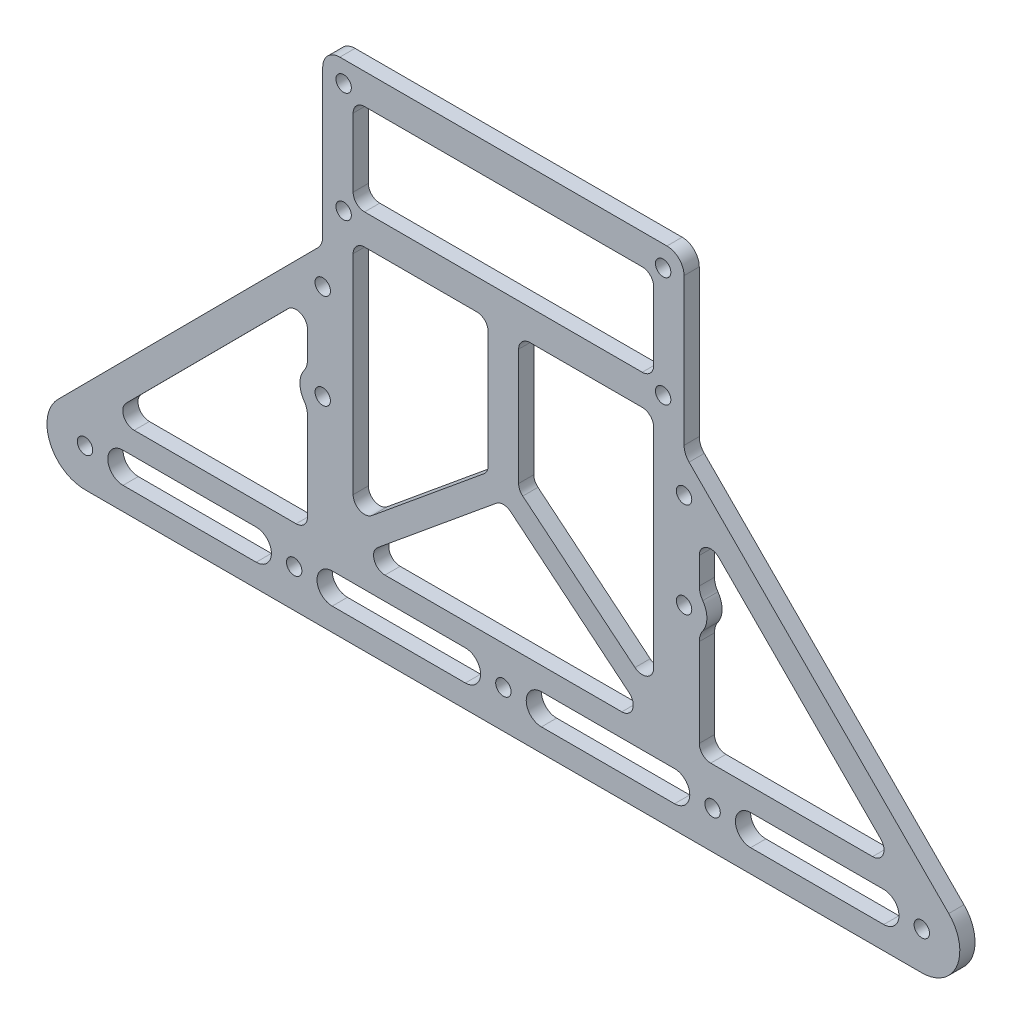
SolidWorks part; units mm, degrees
material "Thornel Mat VMA"
ref_plane "前视基准面" through (0, 0, 0) normal (0, 0, 1) x (1, 0, 0)
ref_plane "上视基准面" through (0, 0, 0) normal (0, 1, 0) x (1, 0, 0)
ref_plane "右视基准面" through (0, 0, 0) normal (1, 0, 0) x (0, 0, -1)
other "Configuration Table"
sketch "草图1" plane through (0, 0, 0) normal (0, 0, 1) x (1, 0, 0)
  line L0 (0, -34.5287) -> (0, -50034.5287) construction
  line L1 (-47.5, -20) -> (47.5, -20)
  line L2 (-47.5, -20) -> (-47.5, 20)
  line L3 (-47.5, 20) -> (47.5, 20)
  line L4 (47.5, -20) -> (47.5, 20)
  line L5 (-47.5, -20) -> (47.5, 20) construction
  line L6 (-47.5, 20) -> (47.5, -20) construction
  line L7 (-42, -14.5) -> (42, -14.5) construction
  line L8 (-42, -14.5) -> (-42, 14.5) construction
  line L9 (-42, 14.5) -> (42, 14.5) construction
  line L10 (42, -14.5) -> (42, 14.5) construction
  line L11 (-42, -14.5) -> (42, 14.5) construction
  line L12 (-42, 14.5) -> (42, -14.5) construction
  line L13 (-47.5, -20) -> (-47.5, -25)
  line L18 (110, -102) -> (-110, -102) construction
  line L19 (110, -112) -> (-110, -112)
  line L20 (-47.5, -25) -> (-117.0892, -94.9471)
  line L21 (110, -92) -> (-110, -92)
  line L22 (47.5, -25) -> (117.0892, -94.9471)
  line L23 (47.5, -20) -> (47.5, -25)
  circle A0 centre (-42, 14.5) radius 2.025
  circle A1 centre (42, 14.5) radius 2.025
  circle A2 centre (42, -14.5) radius 2.025
  circle A3 centre (-42, -14.5) radius 2.025
  circle A4 centre (-42, 14.5) radius 5.5 construction
  arc A5 (110, -112) -> (110, -92) centre (110, -102) ccw
  arc A6 (-110, -92) -> (-110, -112) centre (-110, -102) ccw
  circle A7 centre (-110, -102) radius 2.025
  circle A8 centre (-55, -102) radius 2.025
  circle A9 centre (0, -102) radius 2.025
  circle A10 centre (55, -102) radius 2.025
  circle A11 centre (110, -102) radius 2.025
  point P0 (0, 0)
  point P6 (0, 0)
  point P17 (0, -102)
  point P20 (0, -102)
  dimension "D3" = 4.05
  dimension "D7" = 11
  dimension "D8" = 5
  dimension "D6" = 4.05
  dimension "D1" = 40
  dimension "D2" = 95
  dimension "D4" = 220
  dimension "D5" = 20
  dimension "D9" = 92
  dimension "D10" = 5
extrude "凸台-拉伸1" add sketch "草图1" along normal blind 4 contours L1 L4 L3 L2 A3 A2 A1 A0 | A6 L21 A5 L22 L23 L1 L13 L20 | L21 A6 L19 A5 A11 A10 A9 A8 A7
fillet "圆角1" radius 4.5 4 edges at (-47.5, -25, 2) (47.5, 20, 2) (47.5, -25, 2) (-47.5, 20, 2)
sketch "草图2" plane through (0, 0, 4) normal (0, 0, 1) x (1, 0, 0)
  line L0 (-43, 20) -> (43, 20) construction
  line L1 (-39.5, -12) -> (39.5, -12)
  line L2 (-39.5, -12) -> (-39.5, 12)
  line L3 (-39.5, 12) -> (39.5, 12)
  line L4 (39.5, -12) -> (39.5, 12)
  line L5 (-39.5, -12) -> (39.5, 12) construction
  line L6 (-39.5, 12) -> (39.5, -12) construction
  line L7 (-47.5, -23.1428) -> (-47.5, 15.5) construction
  line L8 (0, 0) -> (0, -50000) construction
  line L9 (-39.5, -20) -> (-4, -20)
  line L10 (-4, -20) -> (-4, -55)
  line L11 (-4, -55) -> (-39.5, -84.2281)
  line L12 (-39.5, -84.2281) -> (-39.5, -20)
  line L13 (0, -59.4786) -> (-39.5, -92)
  line L14 (-39.5, -92) -> (39.5, -92)
  line L15 (0, -92) -> (0, -59.4786)
  line L16 (110, -112) -> (-110, -112) construction
  line L17 (-39.5, -84.2281) -> (-39.5, -92) construction
  line L18 (-51.5, -38.9456) -> (-104.283, -92)
  line L19 (-104.283, -92) -> (-51.5, -92)
  line L20 (-51.5, -92) -> (-51.5, -38.9456)
  line L21 (-48.8099, -26.3166) -> (-117.0892, -94.9471) construction
  line L22 (104.283, -92) -> (51.5, -92)
  line L23 (51.5, -38.9456) -> (104.283, -92)
  line L24 (51.5, -92) -> (51.5, -38.9456)
  line L25 (0, -59.4786) -> (39.5, -92)
  line L26 (4, -55) -> (39.5, -84.2281)
  line L27 (4, -20) -> (4, -55)
  line L28 (39.5, -20) -> (4, -20)
  line L29 (39.5, -84.2281) -> (39.5, -20)
  line L30 (-110, -102) -> (-55, -102) construction
  line L31 (-100, -102) -> (-65, -102) construction
  line L32 (-100, -98) -> (-65, -98)
  line L33 (-100, -106) -> (-65, -106)
  line L34 (-45, -102) -> (-10, -102) construction
  line L35 (-45, -98) -> (-10, -98)
  line L36 (-45, -106) -> (-10, -106)
  line L37 (10, -102) -> (45, -102) construction
  line L38 (10, -98) -> (45, -98)
  line L39 (10, -106) -> (45, -106)
  line L40 (65, -102) -> (100, -102) construction
  line L41 (65, -98) -> (100, -98)
  line L42 (65, -106) -> (100, -106)
  line L43 (55, -102) -> (110, -102) construction
  arc A0 (-100, -98) -> (-100, -106) centre (-100, -102) ccw
  arc A1 (-65, -106) -> (-65, -98) centre (-65, -102) ccw
  arc A2 (-45, -98) -> (-45, -106) centre (-45, -102) ccw
  arc A3 (-10, -106) -> (-10, -98) centre (-10, -102) ccw
  arc A4 (10, -98) -> (10, -106) centre (10, -102) ccw
  arc A5 (45, -106) -> (45, -98) centre (45, -102) ccw
  arc A6 (65, -98) -> (65, -106) centre (65, -102) ccw
  arc A7 (100, -106) -> (100, -98) centre (100, -102) ccw
  point P0 (0, 0)
  point P40 (-82.5, -102)
  point P48 (-27.5, -102)
  point P55 (27.5, -102)
  point P62 (82.5, -102)
  point P71 (82.5, -102)
  dimension "D11" = 6
  dimension "D1" = 8
  dimension "D2" = 8
  dimension "D3" = 20
  dimension "D4" = 6
  dimension "D5" = 8
  dimension "D6" = 4
  dimension "D7" = 7
  dimension "D8" = 12
  dimension "D9" = 35
  dimension "D10" = 35
  dimension "D12" = 4
extrude "切除-拉伸1" cut sketch "草图2" against normal blind 10 contours L1 L4 L3 L2 | L12 L11 L10 L9 | L26 L29 L28 L27 | L25 L15 L14 | L14 L15 L13 | L24 L22 L23 | L19 L20 L18 | L33 A1 L32 A0 | L36 A3 L35 A2 | L39 A5 L38 A4 | L42 A7 L41 A6
fillet "圆角2" radius 3 21 edges at (51.5, -38.9456, 2) (104.283, -92, 2) (51.5, -92, 2) (-39.5, -20, 2) (-4, -20, 2) (-4, -55, 2) (-39.5, -84.2281, 2) (-51.5, -38.9456, 2) (-51.5, -92, 2) (-104.283, -92, 2) (4, -20, 2) (39.5, -20, 2) (39.5, -84.2281, 2) (4, -55, 2) (39.5, -92, 2) (-39.5, -92, 2) (0, -59.4786, 2) (39.5, 12, 2) (39.5, -12, 2) (-39.5, -12, 2) (-39.5, 12, 2)
sketch "草图3" plane through (0, 0, 4) normal (0, 0, 1) x (1, 0, 0)
  line L0 (-47.5, -112) -> (-47.5, -59.5) construction
  line L1 (110, -112) -> (-110, -112) construction
  line L3 (47.5, -34.5) -> (-47.5, -34.5) construction
  line L4 (47.5, -34.5) -> (47.5, -59.5) construction
  line L5 (47.5, -59.5) -> (-47.5, -59.5) construction
  line L6 (-47.5, -34.5) -> (-47.5, -59.5) construction
  line L7 (47.5, -34.5) -> (-47.5, -59.5) construction
  line L8 (47.5, -59.5) -> (-47.5, -34.5) construction
  line L10 (0, 0) -> (0, -47) construction
  circle A0 centre (-47.5, -34.5) radius 2.025
  circle A1 centre (-47.5, -59.5) radius 2.025
  circle A2 centre (47.5, -34.5) radius 2.025
  circle A3 centre (47.5, -59.5) radius 2.025
  point P4 (0, -47)
  dimension "D4" = 4.05
  dimension "D1" = 52.5
  dimension "D2" = 25
  dimension "D3" = 95
extrude "切除-拉伸2" cut sketch "草图3" against normal blind 10
sketch "草图4" plane through (0, 0, 4) normal (0, 0, 1) x (1, 0, 0)
  circle A0 centre (-47.5, -59.5) radius 6
  circle A1 centre (47.5, -59.5) radius 6
  circle A2 centre (47.5, -59.5) radius 2.025 construction
  circle A3 centre (-47.5, -59.5) radius 2.025 construction
  circle A4 centre (47.5, -59.5) radius 2.025
  circle A5 centre (-47.5, -59.5) radius 2.025
  dimension "D1" = 12
extrude "凸台-拉伸2" add sketch "草图4" against normal up to surface (4 mm away) up to face at (-45.475, -59.5, 0)
fillet "圆角3" radius 5 4 edges at (-51.5, -55.0279, 2) (-51.5, -63.9721, 2) (51.5, -55.0279, 2) (51.5, -63.9721, 2)
